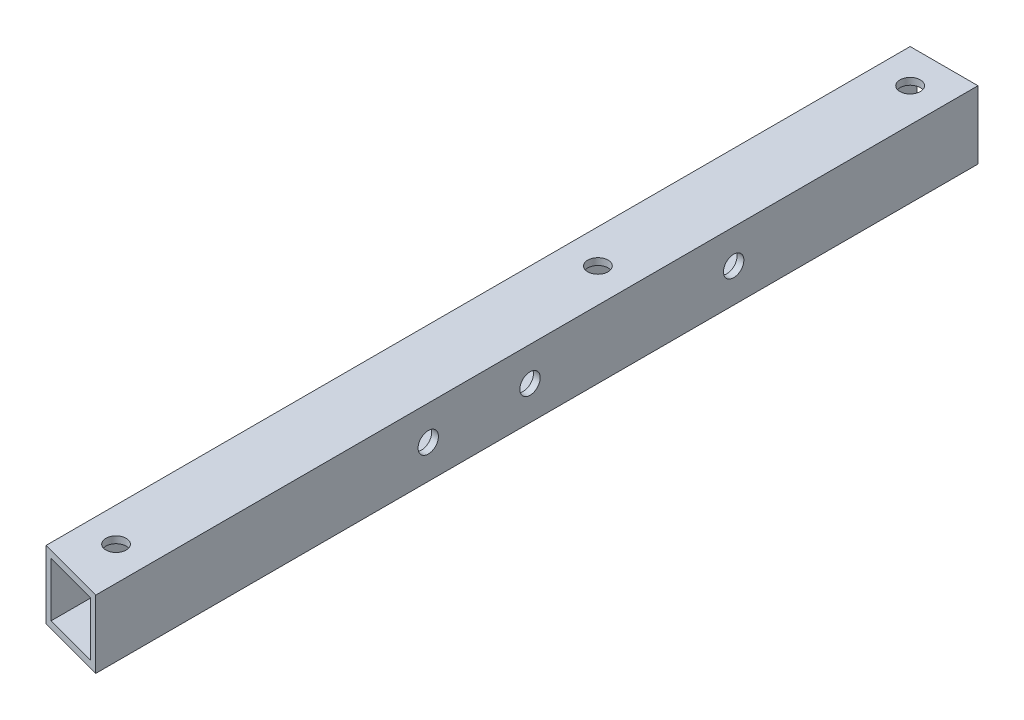
SolidWorks part; units mm, degrees
material "6063-O"
ref_plane "前视基准面" through (0, 0, 0) normal (0, 0, 1) x (1, 0, 0)
ref_plane "上视基准面" through (0, 0, 0) normal (0, 1, 0) x (1, 0, 0)
ref_plane "右视基准面" through (0, 0, 0) normal (1, 0, 0) x (0, 0, -1)
other "Configuration Table"
sketch "草图1" plane through (0, 0, 0) normal (0, 0, 1) x (1, 0, 0)
  line L1 (5, 5) -> (-5, 5)
  line L2 (5, 5) -> (5, -5)
  line L3 (5, -5) -> (-5, -5)
  line L4 (-5, 5) -> (-5, -5)
  line L5 (5, 5) -> (-5, -5) construction
  line L6 (5, -5) -> (-5, 5) construction
  point P4 (0, 0)
  dimension "D1" = 10
  dimension "D2" = 10
extrude "拉伸-薄壁1" add sketch "草图1" along normal blind 130 thin thin type one direction reverse wall 1
sketch "草图2" plane through (0, -5, 0) normal (0, -1, 0) x (1, 0, 0)
  line L0 (0, 0) -> (0, 130) construction
  line L1 (-5, 0) -> (5, 0) construction
  line L2 (-5, 130) -> (5, 130) construction
  line L3 (5, 130) -> (-5, 127.3205)
  line L4 (-5, 130) -> (-5, 0) construction
  line L5 (-5, 127.3205) -> (-5, 130)
  line L6 (-5, 130) -> (5, 130)
  line L7 (-5, 127.3205) -> (5, 127.3205) construction
  line L8 (5, 130) -> (5, 0) construction
  circle A0 centre (0, 51) radius 1.5
  circle A2 centre (0, 122) radius 1.5
  circle A4 centre (0, 5) radius 1.5
  dimension "D2" = 3
  dimension "D5" = 8
  dimension "D8" = 5
  dimension "D1" = 15
  dimension "D3" = 51
extrude "切除-拉伸1" cut sketch "草图2" against normal through all
sketch "草图3" plane through (5, 0, 0) normal (1, 0, 0) x (0, 0, -1)
  line L0 (0, 0) -> (-130, 0) construction
  line L1 (0, -5) -> (0, 5) construction
  line L2 (-130, -5) -> (-130, 5) construction
  circle A0 centre (-36, 0) radius 1.5
  circle A1 centre (-66, 0) radius 1.5
  circle A2 centre (-81, 0) radius 1.5
  dimension "D1" = 3
  dimension "D3" = 30
  dimension "D5" = 15
  dimension "D2" = 36
extrude "切除-拉伸2" cut sketch "草图3" against normal through all
